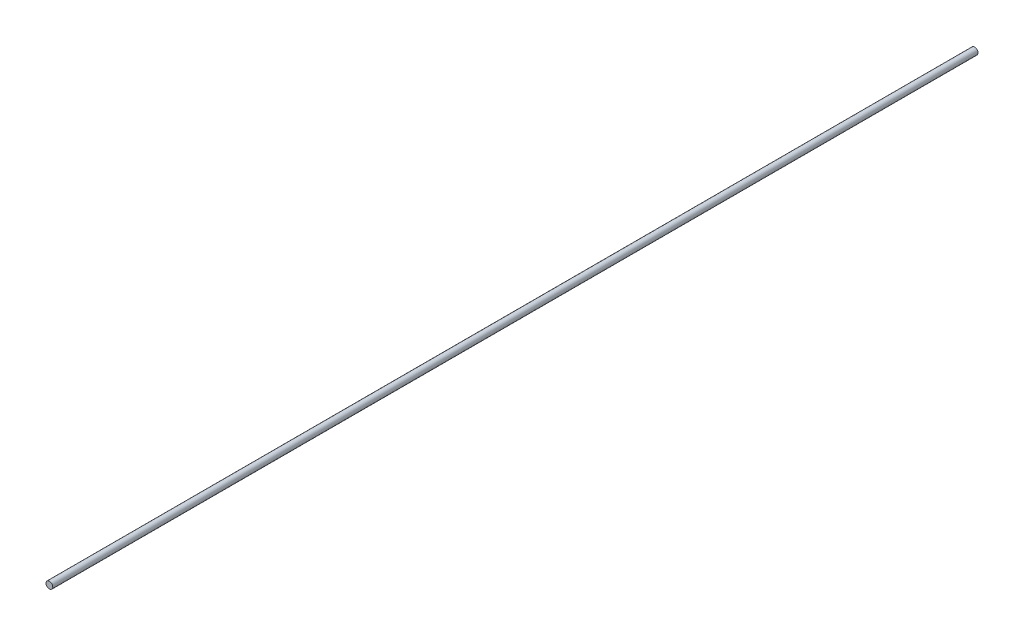
SolidWorks part; units mm, degrees
material "Stainless Steel (ferritic)"
ref_plane "Front Plane" through (0, 0, 0) normal (0, 0, 1) x (1, 0, 0)
ref_plane "Top Plane" through (0, 0, 0) normal (0, 1, 0) x (1, 0, 0)
ref_plane "Right Plane" through (0, 0, 0) normal (1, 0, 0) x (0, 0, -1)
sketch "Sketch1" plane through (0, 0, 0) normal (0, 0, 1) x (1, 0, 0)
  circle A0 centre (0, 0) radius 1.5
  dimension "D1" = 3
extrude "Boss-Extrude1" add sketch "Sketch1" along normal blind 410
